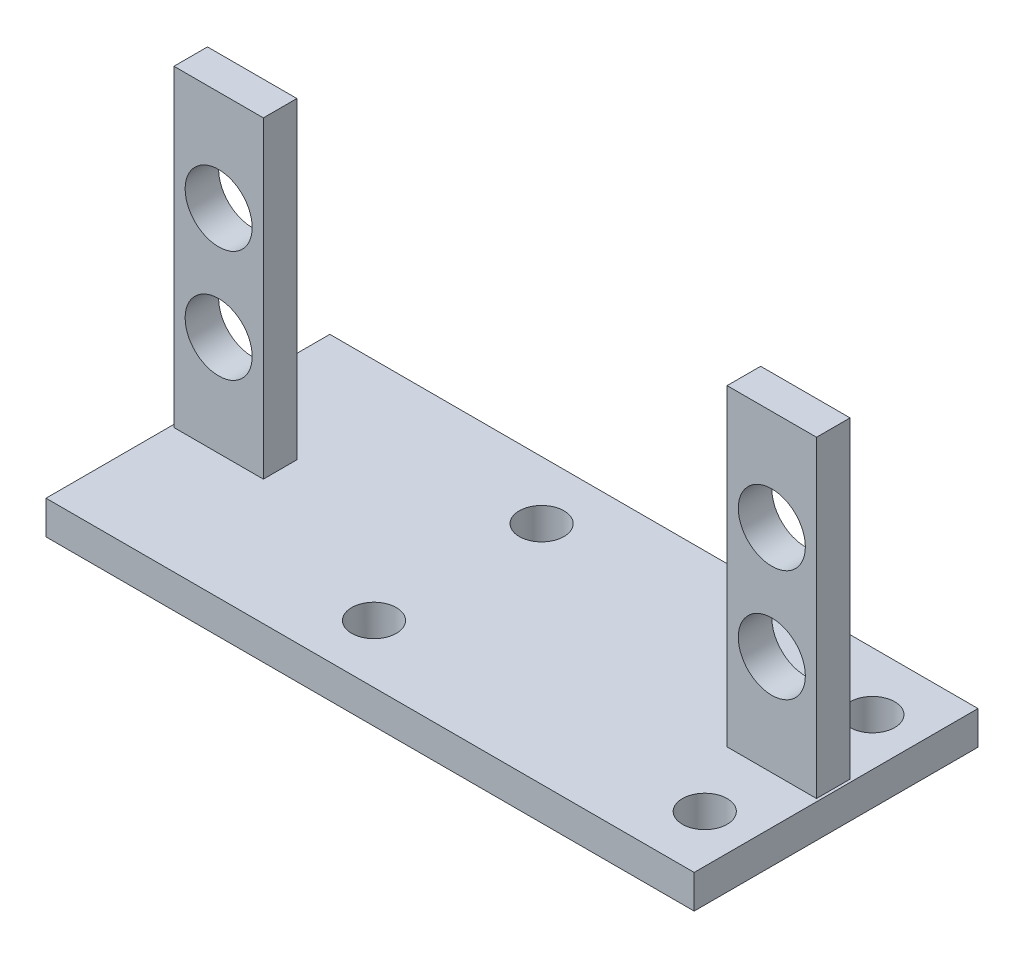
SolidWorks part; units mm, degrees
material "ABS"
ref_plane "Front" through (0, 0, 0) normal (0, 0, 1) x (1, 0, 0)
ref_plane "Top" through (0, 0, 0) normal (0, 1, 0) x (1, 0, 0)
ref_plane "Right" through (0, 0, 0) normal (1, 0, 0) x (0, 0, -1)
sketch "草图1" plane through (0, 0, 0) normal (0, 1, 0) x (1, 0, 0)
  line L0 (0, 0) -> (0, 12.7) construction
  line L1 (0, 0) -> (0, -12.7) construction
  line L2 (0, 0) -> (29, 0) construction
  line L3 (-29, 12.7) -> (29, 12.7)
  line L4 (29, 12.7) -> (29, -12.7)
  line L5 (-29, 12.7) -> (-29, -12.7)
  line L6 (-29, -12.7) -> (29, -12.7)
  point P10 (-29, 0)
extrude "凸台-拉伸1" add sketch "草图1" along normal blind 3
sketch "草图2" plane through (0, 3, 0) normal (0, 1, 0) x (1, 0, 0)
  line L0 (0, 12.7) -> (24.75, 12.7) construction
  line L1 (29, 12.7) -> (-29, 12.7) construction
  line L2 (0, 12.7) -> (-24.75, 12.7) construction
  line L3 (-24.75, 12.7) -> (-24.75, 9.7) construction
  line L4 (-24.75, 9.7) -> (-28.75, 9.7) construction
  line L5 (-24.75, 9.7) -> (-20.75, 9.7) construction
  line L6 (24.75, 12.7) -> (24.75, 9.7) construction
  line L7 (24.75, 9.7) -> (28.75, 9.7) construction
  line L8 (24.75, 9.7) -> (20.75, 9.7) construction
  line L9 (-20.75, 9.7) -> (-28.75, 9.7)
  line L10 (-28.75, 9.7) -> (-28.75, 12.7)
  line L11 (-28.75, 12.7) -> (-20.75, 12.7)
  line L12 (-20.75, 12.7) -> (-20.75, 9.7)
  line L13 (20.75, 9.7) -> (28.75, 9.7)
  line L14 (28.75, 9.7) -> (28.75, 12.7)
  line L15 (28.75, 12.7) -> (20.75, 12.7)
  line L16 (20.75, 12.7) -> (20.75, 9.7)
  line L17 (-20.75, 0) -> (-20.75, 1.5) construction
  line L18 (-20.75, 1.5) -> (-28.75, 1.5) construction
  line L19 (-28.75, 1.5) -> (-28.75, -1.5) construction
  line L20 (-28.75, -1.5) -> (-20.75, -1.5) construction
  line L21 (-20.75, -1.5) -> (-20.75, 0) construction
  line L22 (0, 0) -> (0, 4.2412) construction
  line L23 (-28.75, 1.5) -> (-20.75, 1.5)
  line L24 (-20.75, 1.5) -> (-20.75, -1.5)
  line L25 (-20.75, -1.5) -> (-28.75, -1.5)
  line L26 (-28.75, -1.5) -> (-28.75, 1.5)
  line L27 (28.75, -1.5) -> (28.75, 1.5)
  line L28 (20.75, -1.5) -> (28.75, -1.5)
  line L29 (20.75, 1.5) -> (20.75, -1.5)
  line L30 (28.75, 1.5) -> (20.75, 1.5)
extrude "凸台-拉伸2" add sketch "草图2" along normal blind 28
sketch "草图3" plane through (0, 0, -9.7) normal (0, 0, 1) x (1, 0, 0)
  line L0 (-24.75, 17) -> (-20.75, 17) construction
  line L2 (-24.75, 17) -> (-24.75, 22) construction
  line L3 (-20.75, 31) -> (-20.75, 3) construction
  line L4 (-24.75, 17) -> (-24.75, 12) construction
  line L5 (0, 0) -> (0, 3) construction
  line L6 (-29, 3) -> (29, 3) construction
  circle A0 centre (-24.75, 12) radius 3
  circle A1 centre (-24.75, 22) radius 3
  circle A2 centre (24.75, 12) radius 3
  circle A3 centre (24.75, 22) radius 3
extrude "切除-拉伸1" cut sketch "草图3" against normal mid plane 24
sketch "草图4" plane through (0, 3, 0) normal (0, 1, 0) x (1, 0, 0)
  line L0 (0, 0) -> (24.75, 0) construction
  line L1 (24.75, 0) -> (24.75, 12.7) construction
  line L2 (28.75, 12.7) -> (20.75, 12.7) construction
  line L3 (24.75, 12.7) -> (9.95, 12.7) construction
  line L4 (20.75, 12.7) -> (-20.75, 12.7) construction
  line L5 (9.95, 12.7) -> (9.95, 0) construction
  line L6 (9.95, 0) -> (9.95, -12.7) construction
  line L7 (-29, -12.7) -> (29, -12.7) construction
  line L8 (9.95, 6.35) -> (-4.85, 6.35) construction
  line L9 (24.75, 0) -> (24.75, -7.5) construction
  circle A4 centre (24.75, -7.5) radius 2
  circle A5 centre (24.75, 7.5) radius 2
  circle A6 centre (-4.85, 7.5) radius 2
  circle A7 centre (-4.85, -7.5) radius 2
extrude "切除-拉伸2" cut sketch "草图4" against normal blind 22
sketch "草图8" plane through (0, 31, 0) normal (0, 1, 0) x (1, 0, 0)
  line L0 (-28.75, 12.7) -> (-28.75, 9.7)
  line L1 (-28.75, 9.7) -> (-20.75, 9.7)
  line L2 (-20.75, 9.7) -> (-20.75, 12.7)
  line L3 (-20.75, 12.7) -> (-28.75, 12.7)
  line L4 (20.75, 12.7) -> (20.75, 9.7)
  line L5 (20.75, 9.7) -> (28.75, 9.7)
  line L6 (28.75, 9.7) -> (28.75, 12.7)
  line L7 (28.75, 12.7) -> (20.75, 12.7)
extrude "切除-拉伸3" cut sketch "草图8" against normal blind 28
